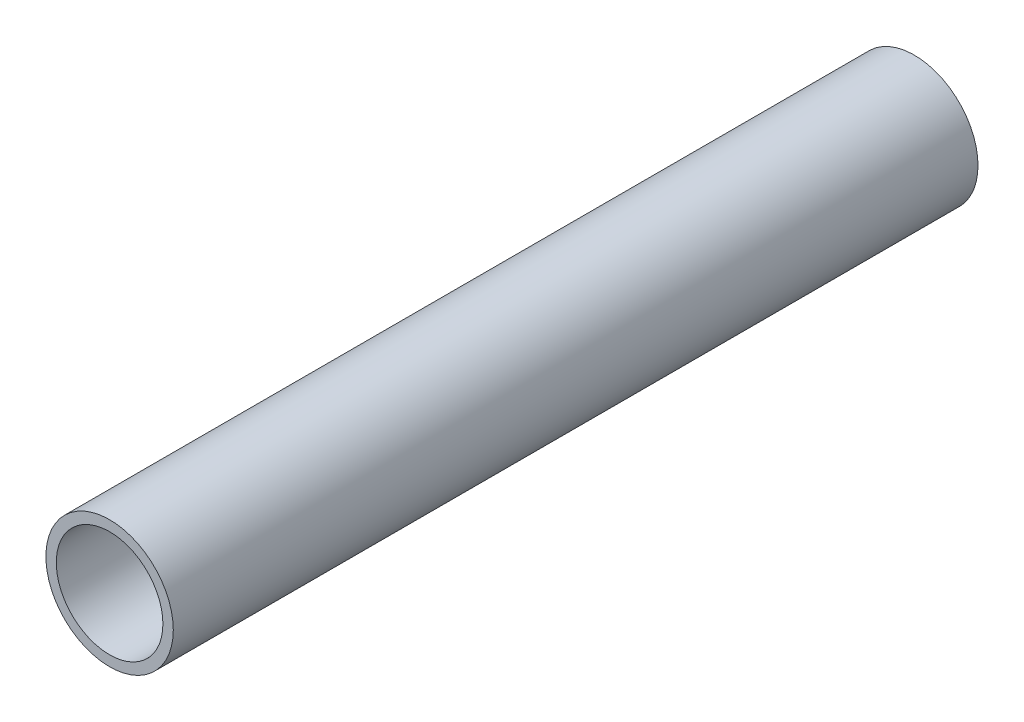
SolidWorks part; units mm, degrees
ref_plane "Front Plane" through (0, 0, 0) normal (0, 0, 1) x (1, 0, 0)
ref_plane "Top Plane" through (0, 0, 0) normal (0, 1, 0) x (1, 0, 0)
ref_plane "Right Plane" through (0, 0, 0) normal (1, 0, 0) x (0, 0, -1)
sketch "Sketch1" plane through (0, 0, 0) normal (0, 0, 1) x (1, 0, 0)
  circle A0 centre (0, 0) radius 24.13
  circle A1 centre (0, 0) radius 20.193
extrude "Boss-Extrude1" add sketch "Sketch1" along normal blind 304.8
